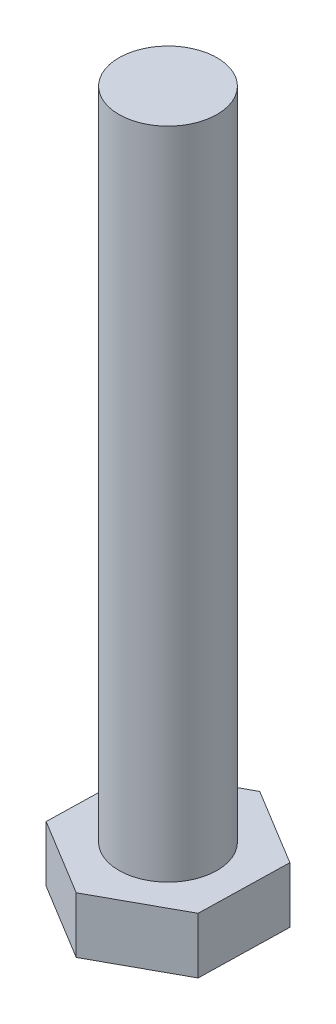
SolidWorks part; units mm, degrees
ref_plane "Спереди" through (0, 0, 0) normal (0, 0, 1) x (1, 0, 0)
ref_plane "Сверху" through (0, 0, 0) normal (0, 1, 0) x (1, 0, 0)
ref_plane "Справа" through (0, 0, 0) normal (1, 0, 0) x (0, 0, -1)
sketch "Эскиз1" plane through (0, 0, 0) normal (0, 1, 0) x (1, 0, 0)
  line L1 (9.3743, -5.6969) -> (9.6209, 5.2699)
  line L2 (9.6209, 5.2699) -> (0.2465, 10.9669)
  line L3 (0.2465, 10.9669) -> (-9.3743, 5.6969)
  line L4 (-9.3743, 5.6969) -> (-9.6209, -5.2699)
  line L5 (-9.6209, -5.2699) -> (-0.2465, -10.9669)
  line L6 (-0.2465, -10.9669) -> (9.3743, -5.6969)
  circle A0 centre (0, 0) radius 9.5 construction
extrude "Бобышка-Вытянуть1" add sketch "Эскиз1" along normal blind 8
sketch "Эскиз2" plane through (0, 8, 0) normal (0, 1, 0) x (1, 0, 0)
  circle A0 centre (0, 0) radius 6
extrude "Бобышка-Вытянуть2" add sketch "Эскиз2" along normal blind 80
chamfer "Фаска1" distance 2 angle 30 6 edges at (4.9337, 0, -8.1184) (9.4976, 0, 0.2135) (4.5639, 0, 8.3319) (-4.9337, 0, 8.1184) (-9.4976, 0, -0.2135) (-4.5639, 0, -8.3319)
